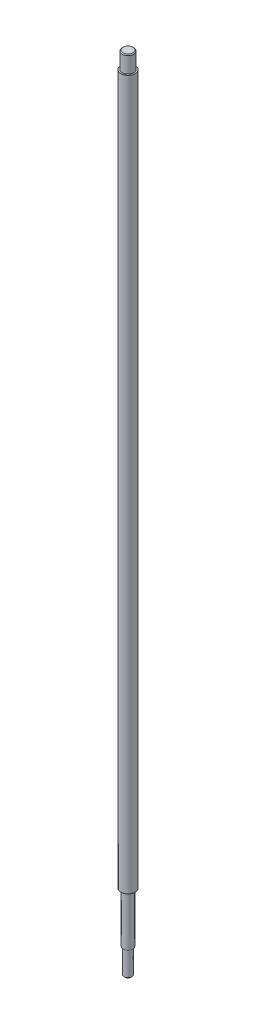
SolidWorks part; units mm, degrees
ref_plane "Front Plane" through (0, 0, 0) normal (0, 0, 1) x (1, 0, 0)
ref_plane "Top Plane" through (0, 0, 0) normal (0, 1, 0) x (1, 0, 0)
ref_plane "Right Plane" through (0, 0, 0) normal (1, 0, 0) x (0, 0, -1)
ref_plane "Plane1" through (0, 0, 0) normal (0, 0, 1) x (1, 0, 0)
sketch "Sketch4" plane through (0, 0, 0) normal (0, 1, 0) x (1, 0, 0)
  circle A0 centre (0, 0) radius 4.2667
  dimension "D1" = 8.5333
extrude "Boss-Extrude1" add sketch "Sketch4" along normal blind 421
sketch "Sketch5" plane through (0, 421, 0) normal (0, 1, 0) x (1, 0, 0)
  circle A0 centre (0, 0) radius 3.4133
  dimension "D1" = 6.8267
extrude "Boss-Extrude2" add sketch "Sketch5" along normal blind 10
chamfer "Chamfer1" distance 0.5 angle 45 1 edges at (0, 431, 3.4133)
sketch "Sketch6" plane through (0, 0, 0) normal (0, -1, 0) x (1, 0, 0)
  circle A0 centre (0, 0) radius 2.8444
  dimension "D1" = 5.6889
extrude "Boss-Extrude3" add sketch "Sketch6" along normal blind 30
sketch "Sketch7" plane through (0, -30, 0) normal (0, -1, 0) x (1, 0, 0)
  circle A0 centre (0, 0) radius 2.2756
  dimension "D1" = 4.5511
extrude "Boss-Extrude4" add sketch "Sketch7" along normal blind 15
chamfer "Chamfer2" distance 0.5 angle 45 1 edges at (0, -45, -2.2756)
scale "Scale1" scale about centroid uniform scaling yes scale factor 7.5
